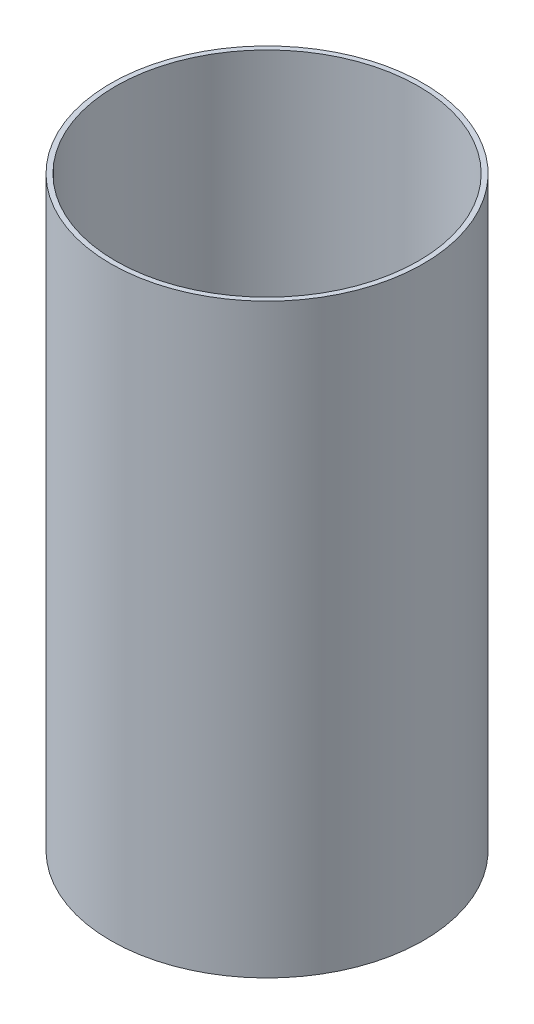
SolidWorks part; units mm, degrees
ref_plane "Front Plane" through (0, 0, 0) normal (0, 0, 1) x (1, 0, 0)
ref_plane "Top Plane" through (0, 0, 0) normal (0, 1, 0) x (1, 0, 0)
ref_plane "Right Plane" through (0, 0, 0) normal (1, 0, 0) x (0, 0, -1)
sketch "Sketch1" plane through (0, 0, 0) normal (0, 1, 0) x (1, 0, 0)
  circle A0 centre (0, 0) radius 98.425
  circle A1 centre (0, 0) radius 101.6
  dimension "D1" = 196.85
  dimension "D2" = 203.2
extrude "Boss-Extrude1" add sketch "Sketch1" along normal blind 381
